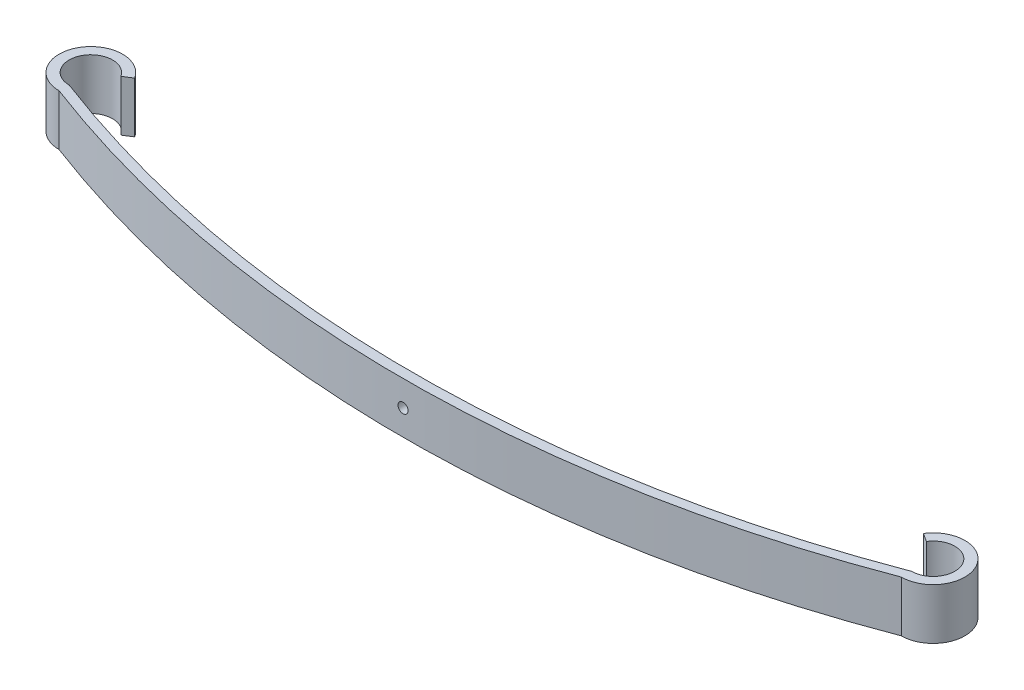
SolidWorks part; units mm, degrees
ref_plane "Front Plane" through (0, 0, 0) normal (0, 0, 1) x (1, 0, 0)
ref_plane "Top Plane" through (0, 0, 0) normal (0, 1, 0) x (1, 0, 0)
ref_plane "Right Plane" through (0, 0, 0) normal (1, 0, 0) x (0, 0, -1)
sketch "Sketch1" plane through (0, 0, 0) normal (0, 1, 0) x (1, 0, 0)
  line L0 (-630, 0) -> (630, 0) construction
  line L1 (-210.8013, -133) -> (245.5549, -133) construction
  line L2 (0, 0) -> (0, -133) construction
  line L3 (-602.5798, 17.4465) -> (-589.9243, 25.4988)
  line L4 (-616.835, -11.5296) -> (-605.5506, -21.4121)
  line L5 (616.835, -11.5296) -> (605.5506, -21.4121)
  line L7 (602.5798, 17.4465) -> (589.9243, 25.4988)
  arc A0 (-616.835, -11.5296) -> (-630, -17.5) centre (-630, 0) ccw
  arc A1 (630, -17.5) -> (616.835, -11.5296) centre (630, 0) ccw
  arc A2 (-630, -17.5) -> (630, -17.5) centre (0, 1642.9318) ccw
  arc A3 (-630.0011, -32.5) -> (630.0011, -32.5) centre (0, 1627.9379) ccw
  arc A4 (-605.5506, -21.4121) -> (-630.0011, -32.5) centre (-630, 0) ccw
  arc A5 (630.0011, -32.5) -> (605.5506, -21.4121) centre (630, 0) ccw
  arc A6 (-630.0217, -47.5) -> (630.0217, -47.5) centre (0, 1613.05) ccw
  arc A7 (630.0217, -47.5) -> (589.9243, 25.4988) centre (630, 0) ccw
  arc A8 (-589.9243, 25.4988) -> (-630.0217, -47.5) centre (-630, 0) ccw
  point P5 (-630.0217, -47.5)
  point P6 (0, -163)
  point P10 (0, -133)
  point P13 (-630.0011, -32.5)
  point P14 (0, -148)
  point P15 (630.0011, -32.5)
  point P20 (630.0217, -47.5)
  dimension "D4" = 35
  dimension "D5" = 35
  dimension "D9" = 15
  dimension "D1" = 133
  dimension "D2" = 630
  dimension "D3" = 630
  dimension "D6" = 15
  dimension "D7" = 15
  dimension "D8" = 15
  dimension "D10" = 15
  dimension "D11" = 15
sketch "Sketch5" plane through (0, 0, 0) normal (0, 0, 1) x (1, 0, 0)
  circle A0 centre (0, 38.1) radius 7.5
  dimension "D2" = 15
  dimension "D1" = 38.1
extrude "Boss-Extrude1" add sketch "Sketch1" along normal blind 76.2 contours L3 A8 A6 A7 L7 A5 A3 A4
sketch "Sketch6" plane through (0, 0, 0) normal (0, 0, 1) x (1, 0, 0)
  circle A0 centre (0, 38.1) radius 7.5
extrude "Cut-Extrude1" cut sketch "Sketch6" along normal through all
